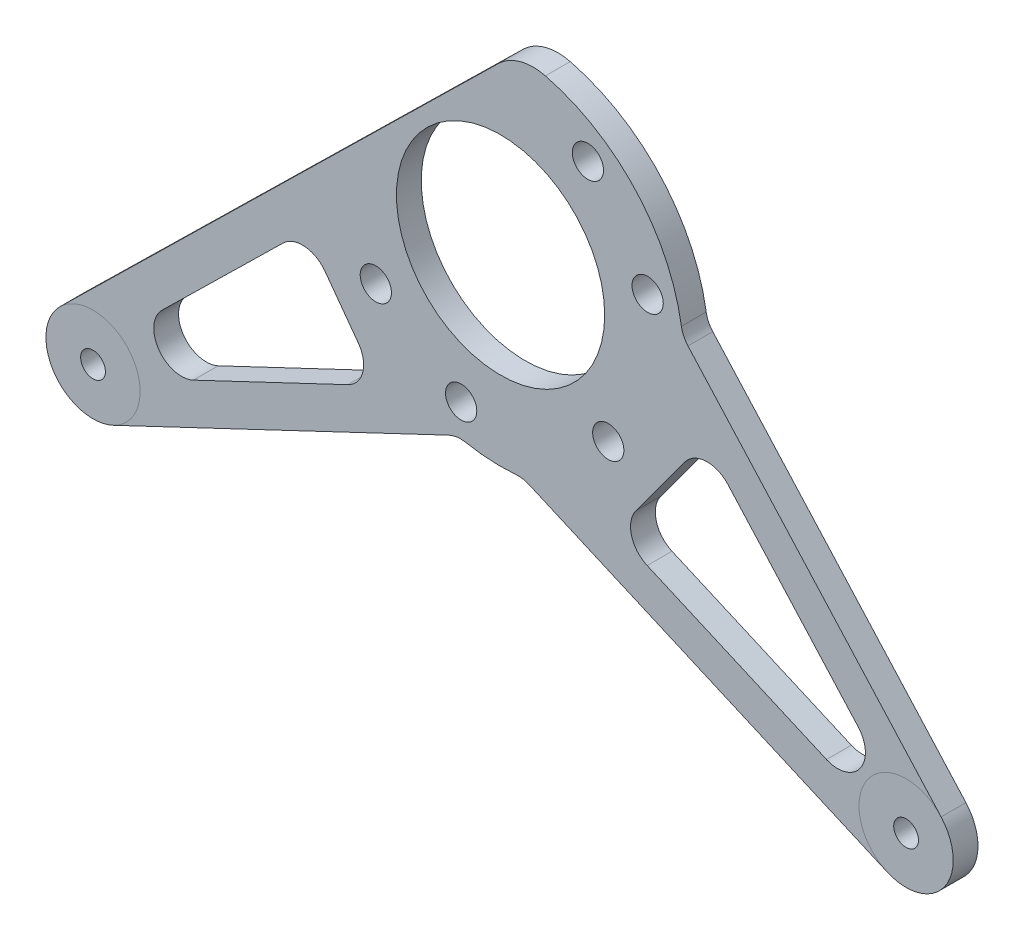
SolidWorks part; units mm, degrees
material "6061-T6 (SS)"
ref_plane "Front Plane" through (0, 0, 0) normal (0, 0, 1) x (1, 0, 0)
ref_plane "Top Plane" through (0, 0, 0) normal (0, 1, 0) x (1, 0, 0)
ref_plane "Right Plane" through (0, 0, 0) normal (1, 0, 0) x (0, 0, -1)
sketch "Motor Plate" plane through (0, 0, 0) normal (0, 0, 1) x (1, 0, 0)
  line L0 (-123.6307, 80.01) -> (-123.6307, -93.98) construction
  line L2 (-123.6307, 80.01) -> (123.3424, 80.01) construction
  line L3 (-123.6307, 80.01) -> (-123.6307, -93.98) construction
  line L4 (-123.6307, -93.98) -> (123.3424, -93.98) construction
  line L5 (123.3424, 80.01) -> (123.3424, -93.98) construction
  line L9 (-123.6307, -81.28) -> (123.3424, -81.28) construction
  line L10 (-110.9307, -81.28) -> (0, 0) construction
  line L12 (-136.3307, 80.01) -> (-136.3307, -93.98) construction
  line L13 (110.6424, 80.01) -> (110.6424, -93.98) construction
  line L14 (-110.9307, 80.01) -> (-110.9307, -93.98) construction
  line L15 (136.0424, 80.01) -> (136.0424, -93.98) construction
  line L16 (0, 0) -> (110.6424, -81.28) construction
  circle A0 centre (0, 0) radius 26.035 construction
  circle A1 centre (0, 0) radius 26.67 construction
  circle A2 centre (0, 0) radius 39 construction
  circle A3 centre (-123.6307, -93.98) radius 12.7 construction
  circle A4 centre (123.3424, -93.98) radius 12.7 construction
  circle A10 centre (-104.3764, -76.4776) radius 3.175 construction
  circle A11 centre (103.862, -76.299) radius 3.175 construction
  circle A12 centre (-123.6307, -93.98) radius 12.7 construction
  circle A13 centre (123.3424, -93.98) radius 12.7 construction
  circle A14 centre (-104.3764, -76.4776) radius 12.065 construction
  circle A15 centre (103.862, -76.299) radius 12.065 construction
  circle A17 centre (-104.3764, -76.4776) radius 3.175 construction
  circle A21 centre (0, 0) radius 111.755 construction
  circle A23 centre (0, 0) radius 103.5 construction
  point P96 (0, 0)
  point P107 (0, 0)
  dimension "D2" = 78
  dimension "D3" = 52.07
  dimension "D9" = 6.35
  dimension "D15" = 24.13
  dimension "D20" = 207
  dimension "D4" = 53.34
  dimension "D11" = 26.0204
  dimension "D12" = 26.3079
  dimension "D13" = 12.7
  dimension "D14" = 12.7
  dimension "D21" = 8.255
sketch "Planetary Inner Plate and Features" plane through (0, 0, 0) normal (0, 0, 1) x (1, 0, 0)
  line L0 (0, 0) -> (0, 82.7651) construction
  line L1 (0, 0) -> (35.7297, 86.2592) construction
  circle A0 centre (0, 0) radius 68 construction
  circle A1 centre (26.0225, 62.8238) radius 3.25
  circle A2 centre (62.8238, 26.0225) radius 3.25
  circle A3 centre (62.8238, -26.0225) radius 3.25
  circle A4 centre (26.0225, -62.8238) radius 3.25
  circle A5 centre (-26.0225, -62.8238) radius 3.25
  circle A6 centre (-62.8238, -26.0225) radius 3.25
  circle A7 centre (-62.8238, 26.0225) radius 3.25
  circle A8 centre (-26.0225, 62.8238) radius 3.25
  circle A9 centre (0, 0) radius 73 construction
  circle A10 centre (0, 0) radius 62.5 construction
  circle A14 centre (0, 0) radius 57 construction
  point P24 (0, 0)
  dimension "D1" = 125
  dimension "D3" = 6.5
  dimension "D5" = 136
  dimension "D6" = 146
  dimension "D7" = 114
  dimension "D2" = 22.5
  dimension "D4" = 8
sketch "Planetary Outer Plate and Features" plane through (0, 0, 0) normal (0, 0, 1) x (1, 0, 0)
  line L0 (-123.6307, 80.01) -> (-123.6307, -93.98) construction
  line L1 (-123.6307, 67.31) -> (-91.8807, 67.31) construction
  line L2 (-123.6307, 67.31) -> (-123.6307, 64.77) construction
  line L3 (-123.6307, 64.77) -> (-91.8807, 64.77) construction
  line L4 (-91.8807, 67.31) -> (-91.8807, 64.77) construction
  line L5 (-123.6307, 80.01) -> (123.3424, 80.01) construction
  line L6 (123.3424, 80.01) -> (123.3424, -93.98) construction
  line L7 (123.3424, 67.31) -> (91.5924, 67.31) construction
  line L8 (123.3424, 67.31) -> (123.3424, 64.77) construction
  line L9 (123.3424, 64.77) -> (91.5924, 64.77) construction
  line L10 (91.5924, 67.31) -> (91.5924, 64.77) construction
  line L11 (-123.6307, 80.01) -> (0, 0) construction
  line L12 (0, 0) -> (123.3424, 80.01) construction
  circle A0 centre (-86.0738, 55.7043) radius 10.16 construction
  circle A4 centre (-86.0738, 55.7043) radius 3.175
  circle A5 centre (-104.3764, -76.4776) radius 10.16 construction
  circle A6 centre (103.862, -76.299) radius 10.16 construction
  circle A19 centre (85.8731, 55.7043) radius 3.175
  circle A23 centre (85.8731, 55.7043) radius 10.16 construction
  dimension "D1" = 20.32
  dimension "D2" = 6.35
  dimension "D3" = 31.75
  dimension "D4" = 2.54
  dimension "D5" = 12.7
  dimension "D6" = 31.75
  dimension "D8" = 12.7
sketch "Sketch3" plane through (0, 0, 0) normal (0, 0, 1) x (1, 0, 0)
  line L0 (0, 0) -> (38.0076, 38.0076) construction
  line L1 (38.0076, 38.0076) -> (0, 0) construction
  line L2 (0, 0) -> (8.4085, 53.0891) construction
  line L3 (8.4085, 53.0891) -> (0, 0) construction
  line L4 (0, 0) -> (53.0891, 8.4085) construction
  line L5 (37.396, 46.1966) -> (46.1966, 37.396)
  line L6 (0, 0) -> (52.2244, 0) construction
  line L7 (37.396, 46.1966) -> (39.5173, 48.3179)
  line L8 (46.1966, 37.396) -> (48.3179, 39.5173)
  line L9 (39.5173, 48.3179) -> (48.3179, 39.5173)
  line L10 (7.7968, 61.2781) -> (16.5975, 52.4775)
  line L11 (7.7968, 61.2781) -> (9.9182, 63.3995)
  line L12 (16.5975, 52.4775) -> (18.7188, 54.5988)
  line L13 (9.9182, 63.3995) -> (18.7188, 54.5988)
  line L14 (52.4775, 16.5975) -> (61.2781, 7.7968)
  line L15 (52.4775, 16.5975) -> (54.5988, 18.7188)
  line L16 (61.2781, 7.7968) -> (63.3995, 9.9182)
  line L17 (54.5988, 18.7188) -> (63.3995, 9.9182)
  line L18 (0, 0) -> (65.3464, 65.3464) construction
  line L19 (48.2398, 3.5592) -> (57.9385, 13.2578) construction
  line L20 (3.5592, 48.2398) -> (13.2578, 57.9385) construction
  line L21 (-22.9925, 58.2068) -> (-11.3132, 38.3928)
  line L22 (-22.9925, 58.2068) -> (-33.3159, 52.1217)
  line L23 (-11.3132, 38.3928) -> (-21.6366, 32.3077)
  line L24 (-33.3159, 52.1217) -> (-21.6366, 32.3077)
  line L25 (-41.8564, 39.3429) -> (-30.1771, 19.5289)
  line L26 (-41.8564, 39.3429) -> (-52.1798, 33.2578)
  line L27 (-30.1771, 19.5289) -> (-40.5005, 13.4438)
  line L28 (-52.1798, 33.2578) -> (-40.5005, 13.4438)
  line L29 (-35.346, 16.4821) -> (0, 0) construction
  line L30 (0, 0) -> (-16.4821, 35.346) construction
  line L31 (-27.5772, 27.5772) -> (0, 0) construction
  line L32 (-104.3764, -76.4776) -> (0, 0) construction
  line L33 (0, 0) -> (103.862, -76.299) construction
  line L34 (47.9914, 3.821) -> (112.8302, -68.2283)
  line L35 (-112.8219, -67.8615) -> (4.07, 46.7159)
  line L36 (-99.2045, -87.3779) -> (-11.0802, -45.565)
  line L37 (99.0326, -87.3553) -> (5.6248, -46.5543)
  line L39 (26.6664, -30.2458) -> (102.1401, -78.9665) construction
  line L41 (29.6834, -30.5805) -> (-103.281, -79.4577) construction
  line L42 (-10.3982, -41.1564) -> (102.8484, -79.3078) construction
  circle A0 centre (8.4085, 53.0891) radius 6.858
  circle A1 centre (38.0076, 38.0076) radius 6.858
  circle A2 centre (53.0891, 8.4085) radius 6.858
  circle A3 centre (0, 0) radius 26.67
  circle A4 centre (-35.346, 16.4821) radius 6
  circle A5 centre (-16.4821, 35.346) radius 6
  circle A6 centre (-27.5772, 27.5772) radius 3.4 construction
  circle A7 centre (0, 0) radius 39 construction
  arc A8 (-46.788, -3.135) -> (4.07, 46.7159) centre (0, 0) ccw
  circle A9 centre (-104.3764, -76.4776) radius 3.175
  circle A10 centre (-31.9469, -22.3695) radius 3.4 construction
  circle A11 centre (22.6625, 32.484) radius 3.4 construction
  circle A12 centre (103.862, -76.299) radius 3.175
  circle A13 centre (38.2896, 10.6389) radius 3.4 construction
  circle A14 centre (-31.9469, -22.3695) radius 3.4
  circle A15 centre (-104.3764, -76.4776) radius 12.065
  circle A16 centre (28.5103, -27.3893) radius 3.4 construction
  circle A17 centre (103.862, -76.299) radius 12.065
  arc A18 (47.9914, 3.821) -> (46.3156, 7.3357) centre (53.0891, 8.4085) cw
  circle A19 centre (-9.3127, -37.9343) radius 3.4 construction
  circle A21 centre (-31.4689, -22.7514) radius 3.4 construction
  circle A23 centre (22.3695, 31.9469) radius 3.4 construction
  circle A24 centre (22.3695, 31.9469) radius 3.4
  arc A25 (-32.2043, 14.8913) -> (-32.3567, 18.0547) centre (-35.2857, 16.3282) ccw
  arc A26 (-19.4151, 33.7847) -> (-17.082, 32.1639) centre (-16.4861, 35.5112) ccw
  circle A27 centre (17.4193, -35.3234) radius 3.4
  circle A28 centre (4.2835, -38.9856) radius 3.4
  circle A29 centre (36.2189, -16.1403) radius 3.4
  circle A30 centre (32.402, 22.9392) radius 3.4
  circle A31 centre (-21.7294, -32.2962) radius 3.4
  circle A32 centre (-38.6821, 3.1211) radius 3.4
  circle A33 centre (-3.3503, 39.1735) radius 3.4
  circle A34 centre (-37.3565, -10.4511) radius 3.4
  circle A35 centre (10.2459, 38.1221) radius 3.4
  arc A36 (41.3345, 0) -> (37.896, 0) centre (39.6152, -2.9333) ccw
  circle A37 centre (22.3695, 31.9469) radius 3.4
  circle A38 centre (22.3695, 31.9469) radius 3.4
  circle A39 centre (37.6711, 10.0939) radius 3.4929
  circle A40 centre (37.6711, 10.0939) radius 3.4929
  circle A41 centre (27.5772, -27.5772) radius 3.4
  circle A42 centre (27.5772, -27.5772) radius 3.4
  circle A43 centre (-10.0939, -37.6711) radius 3.4
  circle A44 centre (-10.0939, -37.6711) radius 3.4
  circle A45 centre (-31.9469, -22.3695) radius 3.4
  circle A46 centre (-31.9469, -22.3695) radius 3.4
  point P79 (-46.788, -3.135)
  dimension "D1" = 13.716
  dimension "D2" = 13.716
  dimension "D3" = 13.716
  dimension "D10" = 53.34
  dimension "D27" = 12
  dimension "D30" = 12
  dimension "D31" = 40
  dimension "D34" = 18
  dimension "D35" = 6.8
  dimension "D36" = 6.35
  dimension "D37" = 24.13
  dimension "D38" = 6.35
  dimension "D39" = 24.13
  dimension "D4" = 36
  dimension "D5" = 36
  dimension "D6" = 3
  dimension "D7" = 53.7509
  dimension "D8" = 53.7509
  dimension "D9" = 53.7509
  dimension "D11" = 45
  dimension "D12" = 3
  dimension "D13" = 3
  dimension "D14" = 12.446
  dimension "D15" = 12.446
  dimension "D16" = 12.446
  dimension "D17" = 62.1089
  dimension "D18" = 6.223
  dimension "D19" = 6.223
  dimension "D20" = 6.223
  dimension "D21" = 5.358
  dimension "D22" = 5.358
  dimension "D23" = 6.223
  dimension "D24" = 5.358
  dimension "D25" = 23
  dimension "D26" = 11.9833
  dimension "D28" = 11.9833
  dimension "D29" = 23
  dimension "D32" = 34
  dimension "D33" = 20
  dimension "D40" = 97.5408
  dimension "D41" = 101.93
sketch "Sketch4" plane through (0, 0, 0) normal (0, 0, 1) x (1, 0, 0)
  line L0 (-112.8219, -67.8615) -> (-0.5157, 42.2211)
  line L1 (-99.2045, -87.3779) -> (-13.269, -46.6036)
  line L2 (47.9914, 3.821) -> (112.8302, -68.2283)
  line L3 (-86.6891, -55.5838) -> (-55.6912, -25.1997)
  line L4 (7.3337, -47.3008) -> (99.0326, -87.3553)
  line L6 (-44.976, -26.0752) -> (-36.4528, -37.7075)
  line L8 (-11.7604, -34.0348) -> (-104.3764, -76.4776) construction
  line L9 (-39.141, -48.3364) -> (-78.662, -67.0882)
  line L10 (-104.3764, -76.4776) -> (-8.7178, -41.4269) construction
  line L12 (-104.3764, -76.4776) -> (0, 0) construction
  line L13 (34.6666, -39.378) -> (47.1951, -22.3236)
  line L14 (29.8771, -24.3045) -> (103.862, -76.299) construction
  line L15 (103.862, -76.299) -> (25.5752, -31.0401) construction
  line L16 (34.5875, 7.5462) -> (103.862, -76.299) construction
  line L17 (103.862, -76.299) -> (40.9336, 12.4083) construction
  line L18 (0, 0) -> (103.862, -76.299) construction
  line L19 (58.2133, -21.7767) -> (91.6161, -58.8942)
  line L21 (83.4828, -70.169) -> (37.5514, -50.106)
  arc A0 (112.8302, -68.2283) -> (99.0326, -87.3553) centre (103.862, -76.299) cw
  arc A1 (47.9914, 3.821) -> (46.3156, 7.3357) centre (53.0891, 8.4085) cw
  arc A2 (46.3156, 7.3357) -> (11.4848, 45.4647) centre (0, 0) ccw
  arc A3 (-112.8219, -67.8615) -> (-99.2045, -87.3779) centre (-104.3764, -76.4776) ccw
  arc A4 (-8.8743, -46.0455) -> (3.896, -46.7308) centre (0, 0) ccw
  circle A5 centre (0, 0) radius 26.67
  circle A6 centre (103.862, -76.299) radius 3.175
  circle A7 centre (-104.3764, -76.4776) radius 3.175
  circle A8 centre (-10.0939, -37.6711) radius 4
  circle A9 centre (-31.9469, -22.3695) radius 4
  arc A10 (3.896, -46.7308) -> (7.3337, -47.3008) centre (4.4869, -53.8182) cw
  circle A11 centre (27.5772, -27.5772) radius 4
  circle A12 centre (37.6711, 10.0939) radius 4
  circle A13 centre (22.3695, 31.9469) radius 4
  arc A14 (-13.269, -46.6036) -> (-8.8743, -46.0455) centre (-10.2203, -53.029) cw
  arc A15 (-0.5157, 42.2211) -> (11.4848, 45.4647) centre (8.3744, 33.1515) cw
  arc A16 (-55.6912, -25.1997) -> (-44.976, -26.0752) centre (-50.7128, -30.2786) cw
  arc A17 (-36.4528, -37.7075) -> (-39.141, -48.3364) centre (-42.1897, -41.911) cw
  arc A18 (-78.662, -67.0882) -> (-86.6891, -55.5838) centre (-81.7107, -60.6628) cw
  arc A19 (34.6666, -39.378) -> (37.5514, -50.106) centre (40.3982, -43.5886) ccw
  arc A20 (47.1951, -22.3236) -> (58.2133, -21.7767) centre (52.9267, -26.5342) cw
  arc A21 (91.6161, -58.8942) -> (83.4828, -70.169) centre (86.3296, -63.6516) cw
  point P48 (5.6248, -46.5543)
  point P51 (-11.0802, -45.565)
  point P55 (4.07, 46.7159)
  dimension "D1" = 53.34
  dimension "D2" = 6.35
  dimension "D3" = 6.35
  dimension "D4" = 46.8929
  dimension "D5" = 8
  dimension "D6" = 8
  dimension "D7" = 8
  dimension "D8" = 7.112
  dimension "D9" = 12.7
  dimension "D10" = 8
  dimension "D11" = 8
  dimension "D13" = 9.525
  dimension "D14" = 12.7
  dimension "D15" = 7.112
  dimension "D17" = 7.112
  dimension "D18" = 9.525
  dimension "D19" = 9.525
  dimension "D21" = 7.112
  dimension "D16" = 7.112
  dimension "D22" = 7.112
  dimension "D23" = 7.112
  dimension "D12" = 9.525
  dimension "D20" = 12.7
extrude "Boss-Extrude1" add sketch "Sketch4" along normal blind 6.35
sketch "Sketch5" plane through (0, 0, 6.35) normal (0, 0, 1) x (1, 0, 0)
  circle A0 centre (-104.3764, -76.4776) radius 12.065
  circle A1 centre (103.862, -76.299) radius 12.065
  dimension "D1" = 24.13
  dimension "D2" = 24.13
sketch "Sketch6" plane through (0, 0, 0) normal (0, 0, -1) x (-1, 0, 0)
  circle A0 centre (-103.862, -76.299) radius 12.065
  circle A1 centre (104.3764, -76.4776) radius 12.065
  dimension "D1" = 24.13
  dimension "D2" = 24.13
split line "Split Line1"
